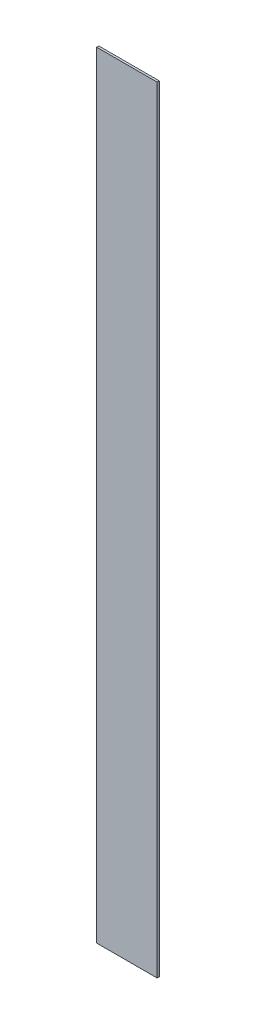
SolidWorks part; units mm, degrees
ref_plane "Front Plane" through (0, 0, 0) normal (0, 0, 1) x (1, 0, 0)
ref_plane "Top Plane" through (0, 0, 0) normal (0, 1, 0) x (1, 0, 0)
ref_plane "Right Plane" through (0, 0, 0) normal (1, 0, 0) x (0, 0, -1)
sketch "Sketch2" plane through (0, 0, 0) normal (0, 0, 1) x (1, 0, 0)
  line L1 (-70, -900) -> (70, -900)
  line L2 (-70, -900) -> (-70, 900)
  line L3 (-70, 900) -> (70, 900)
  line L4 (70, -900) -> (70, 900)
  line L5 (-70, -900) -> (70, 900) construction
  line L6 (-70, 900) -> (70, -900) construction
  point P0 (0, 0)
extrude "Boss-Extrude1" add sketch "Sketch2" along normal blind 5
